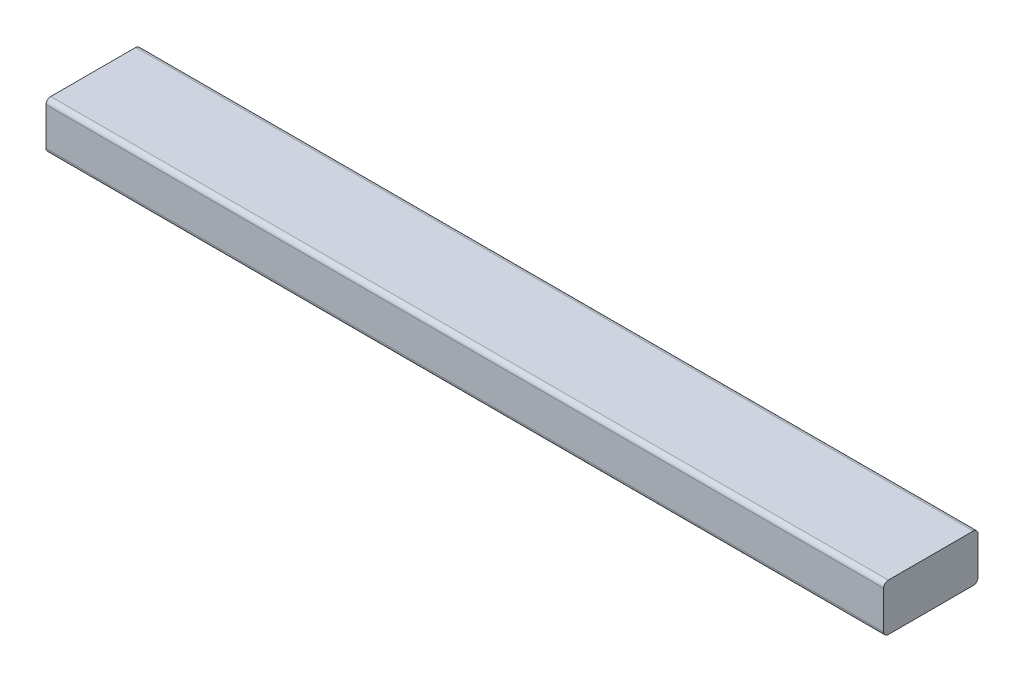
SolidWorks part; units mm, degrees
material "Balsa"
ref_plane "Front Plane" through (0, 0, 0) normal (0, 0, 1) x (1, 0, 0)
ref_plane "Top Plane" through (0, 0, 0) normal (0, 1, 0) x (1, 0, 0)
ref_plane "Right Plane" through (0, 0, 0) normal (1, 0, 0) x (0, 0, -1)
sketch "Sketch1" plane through (0, -12.7, 0) normal (0, -1, 0) x (-1, 0, 0)
  line L0 (-2714.3, -292.78) -> (-2714.3, -384.22) construction
  line L1 (-2714.3, 389.3) -> (-1812.7, 389.3)
  line L2 (-2714.3, 389.3) -> (-2714.3, 287.7)
  line L3 (-2714.3, 287.7) -> (-1812.7, 287.7)
  line L4 (-1812.7, 389.3) -> (-1812.7, 287.7)
  line L5 (-1812.7, -384.22) -> (-1812.7, -292.78) construction
  line L6 (-1803.322, 287.7) -> (-2600, 287.7) construction
  dimension "D1" = 101.6
extrude "Boss-Extrude1" add sketch "Sketch1" against normal blind 50.8
fillet "Fillet1" radius 5.08 4 edges at (2263.5, -12.7, -287.7) (2263.5, -12.7, -389.3) (2263.5, 38.1, -287.7) (2263.5, 38.1, -389.3)
